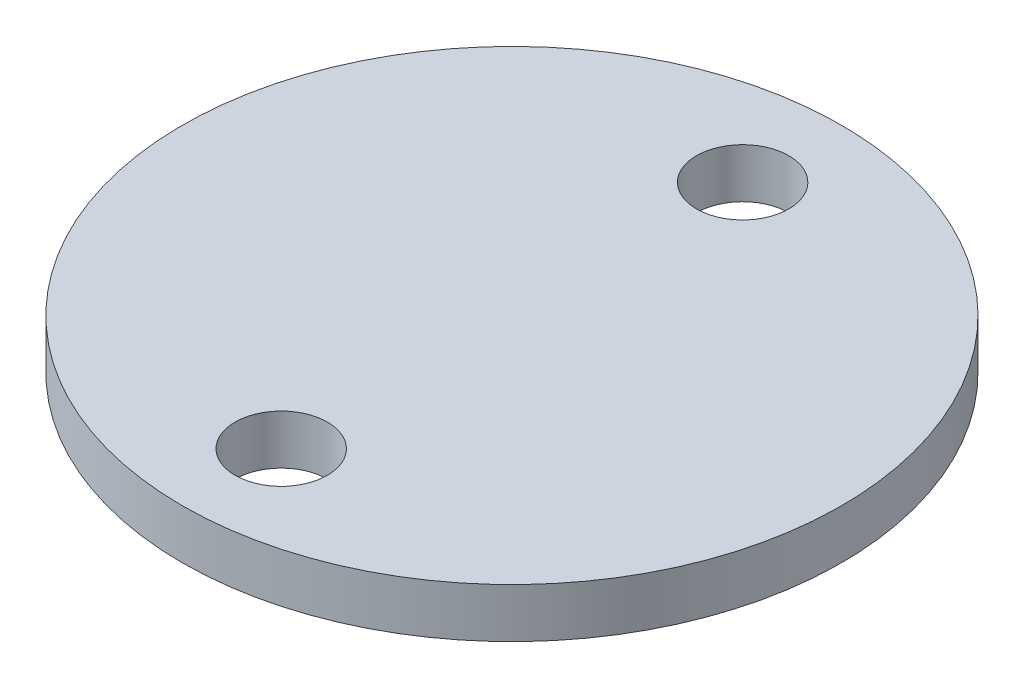
SolidWorks part; units mm, degrees
ref_plane "Front Plane" through (0, 0, 0) normal (0, 0, 1) x (1, 0, 0)
ref_plane "Top Plane" through (0, 0, 0) normal (0, 1, 0) x (1, 0, 0)
ref_plane "Right Plane" through (0, 0, 0) normal (1, 0, 0) x (0, 0, -1)
sketch "Sketch1" plane through (0, 0, 0) normal (0, 1, 0) x (1, 0, 0)
  circle A0 centre (0, 0) radius 10
  dimension "D1" = 20
extrude "Boss-Extrude1" add sketch "Sketch1" against normal blind 1.5
sketch "Sketch2" plane through (0, 0, 0) normal (0, 1, 0) x (1, 0, 0)
  line L0 (0, 7) -> (0, -7) construction
  circle A0 centre (0, -5.5) radius 1.4 construction
  circle A1 centre (0, 5.5) radius 1.4 construction
  circle A2 centre (0, -5.5) radius 1.4 construction
  circle A3 centre (0, 5.5) radius 1.4 construction
  circle A4 centre (0, 7) radius 1.4
  circle A5 centre (0, -7) radius 1.4
  point P10 (0, 0)
  point P14 (0, -6.9)
  dimension "D1" = 14
extrude "Cut-Extrude1" cut sketch "Sketch2" against normal through all
sketch "Sketch3" plane through (0, -1.5, 0) normal (0, -1, 0) x (1, 0, 0)
  line L0 (1.9074, 1.6161) -> (2.0855, -1.3786) construction
  line L1 (1.9074, 1.6161) -> (2.0855, -1.3786) construction
  line L2 (1.9857, 1.6472) -> (2.1669, -1.4003)
  arc A0 (1.9074, 1.6161) -> (2.0855, -1.3786) centre (0, 0) ccw construction
  arc A1 (1.9074, 1.6161) -> (2.0855, -1.3786) centre (0, 0) ccw construction
  arc A2 (1.9857, 1.6472) -> (2.1669, -1.4003) centre (0, 0) ccw
  circle A3 centre (0, 0) radius 3.5
  dimension "D2" = 7
  dimension "D1" = 2.58
extrude "Boss-Extrude2" add sketch "Sketch3" along normal blind 3.5
fillet "Fillet1" radius 0.5 2 edges at (2.0763, -5, 0.1235) (-2.5755, -5, -0.1531)
